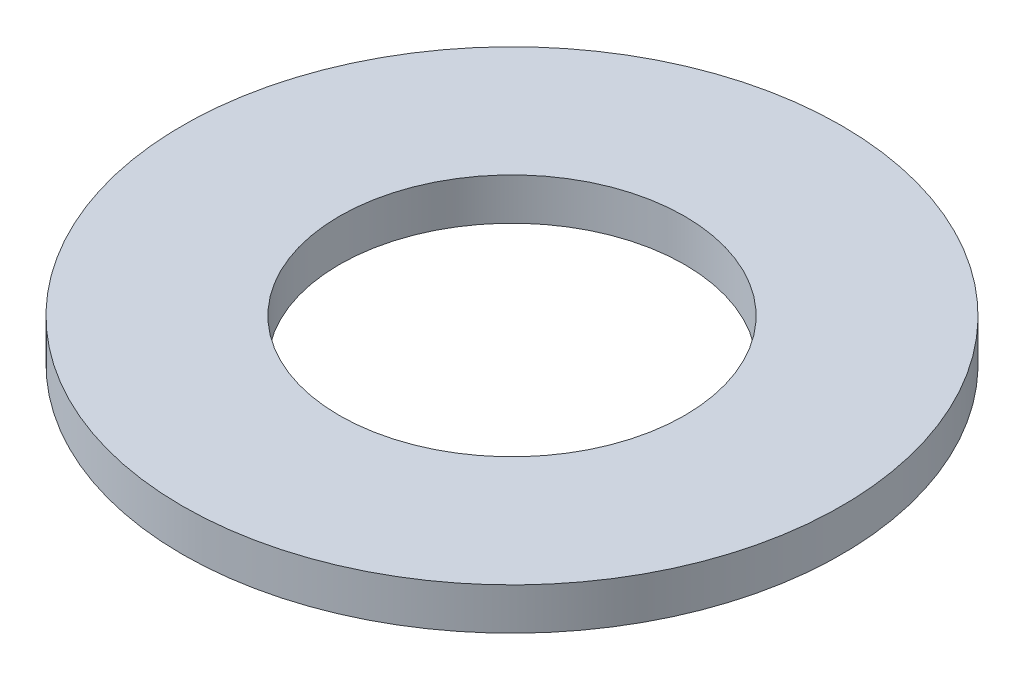
SolidWorks part; units mm, degrees
ref_plane "Front Plane" through (0, 0, 0) normal (0, 0, 1) x (1, 0, 0)
ref_plane "Top Plane" through (0, 0, 0) normal (0, 1, 0) x (1, 0, 0)
ref_plane "Right Plane" through (0, 0, 0) normal (1, 0, 0) x (0, 0, -1)
sketch "Sketch1" plane through (0, 0, 0) normal (0, 1, 0) x (1, 0, 0)
  circle A0 centre (0, 0) radius 7.875
  circle A1 centre (0, 0) radius 4.125
  dimension "D1" = 15.75
  dimension "D2" = 8.25
extrude "Boss-Extrude1" add sketch "Sketch1" along normal blind 1
